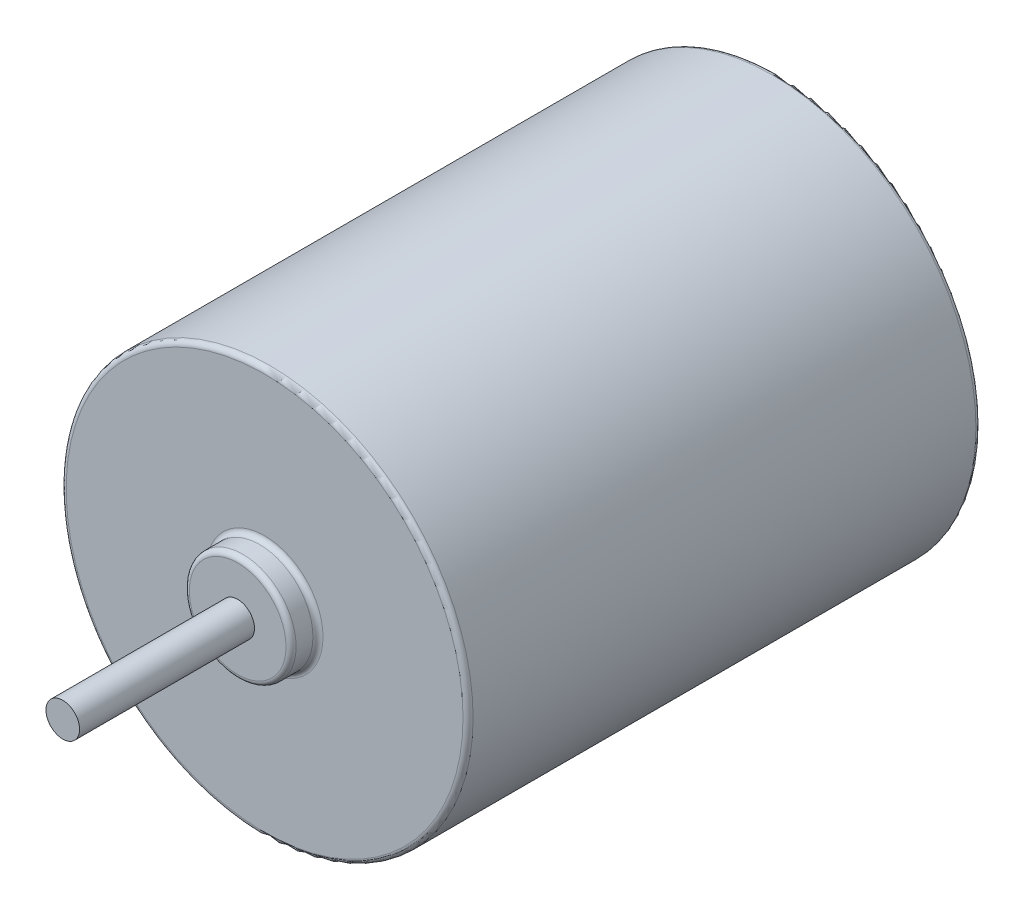
SolidWorks part; units mm, degrees
ref_plane "Front Plane" through (0, 0, 0) normal (0, 0, 1) x (1, 0, 0)
ref_plane "Top Plane" through (0, 0, 0) normal (0, 1, 0) x (1, 0, 0)
ref_plane "Right Plane" through (0, 0, 0) normal (1, 0, 0) x (0, 0, -1)
sketch "Sketch1" plane through (0, 0, 0) normal (0, 0, 1) x (1, 0, 0)
  circle A0 centre (0, 0) radius 12.1
  dimension "D1" = 24.2
extrude "Boss-Extrude1" add sketch "Sketch1" against normal blind 30.5
sketch "Sketch3" plane through (0, 0, 0) normal (0, 0, 1) x (1, 0, 0)
  circle A0 centre (0, 0) radius 3.175
  dimension "D1" = 6.35
extrude "Boss-Extrude2" add sketch "Sketch3" along normal blind 1.6
ref_plane "Plane1" through (0, 0, 1.6) normal (0, 0, 1) x (1, 0, 0)
sketch "Sketch4" plane through (0, 0, 1.6) normal (0, 0, 1) x (1, 0, 0)
  circle A0 centre (0, 0) radius 1
  dimension "D1" = 2
extrude "Boss-Extrude3" add sketch "Sketch4" along normal blind 10.4
ref_plane "Plane2" through (0, 0, -30.5) normal (0, 0, -1) x (-1, 0, 0)
sketch "Sketch5" plane through (0, 0, -30.5) normal (0, 0, -1) x (-1, 0, 0)
  circle A0 centre (0, 0) radius 4.25
  dimension "D1" = 8.5
extrude "Boss-Extrude4" add sketch "Sketch5" along normal blind 2
fillet "Fillet1" radius 0.3 1 edges at (3.175, 0, 0)
fillet "Fillet2" radius 0.3 5 edges at (12.1, 0, -30.5) (-4.25, 0, -30.5) (3.175, 0, 1.6) (-4.25, 0, -32.5) (12.1, 0, 0)
